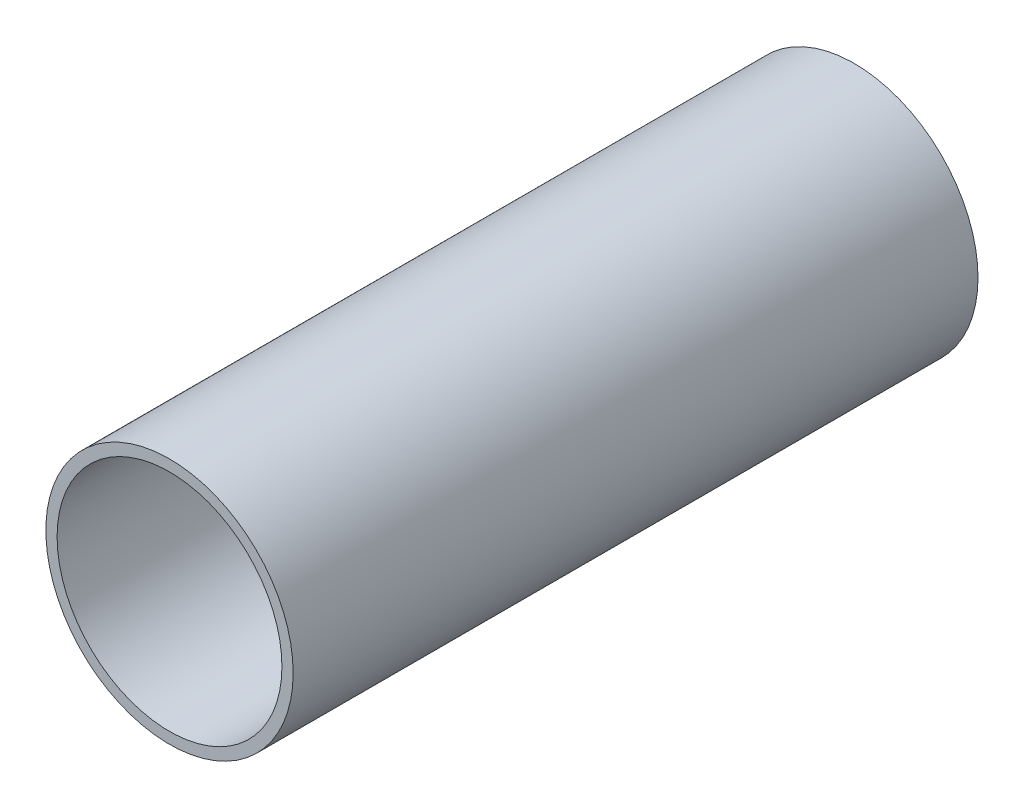
SolidWorks part; units mm, degrees
ref_plane "Front Plane" through (0, 0, 0) normal (0, 0, 1) x (1, 0, 0)
ref_plane "Top Plane" through (0, 0, 0) normal (0, 1, 0) x (1, 0, 0)
ref_plane "Right Plane" through (0, 0, 0) normal (1, 0, 0) x (0, 0, -1)
sketch "Sketch1" plane through (0, 0, 0) normal (1, 0, 0) x (0, 0, -1)
  line L1 (-228.6, 0) -> (-228.6, 82.55)
  line L2 (-228.6, 82.55) -> (228.6, 82.55)
  line L3 (228.6, 82.55) -> (228.6, 0)
  line L4 (-228.6, 0) -> (228.6, 0)
  point P4 (0, 0)
  point P8 (0, 0)
  dimension "D1" = 457.2
  dimension "D2" = 82.55
revolve "Revolve1" add sketch "Sketch1" angle 360 about L4
shell "Shell4" thickness 7.5
